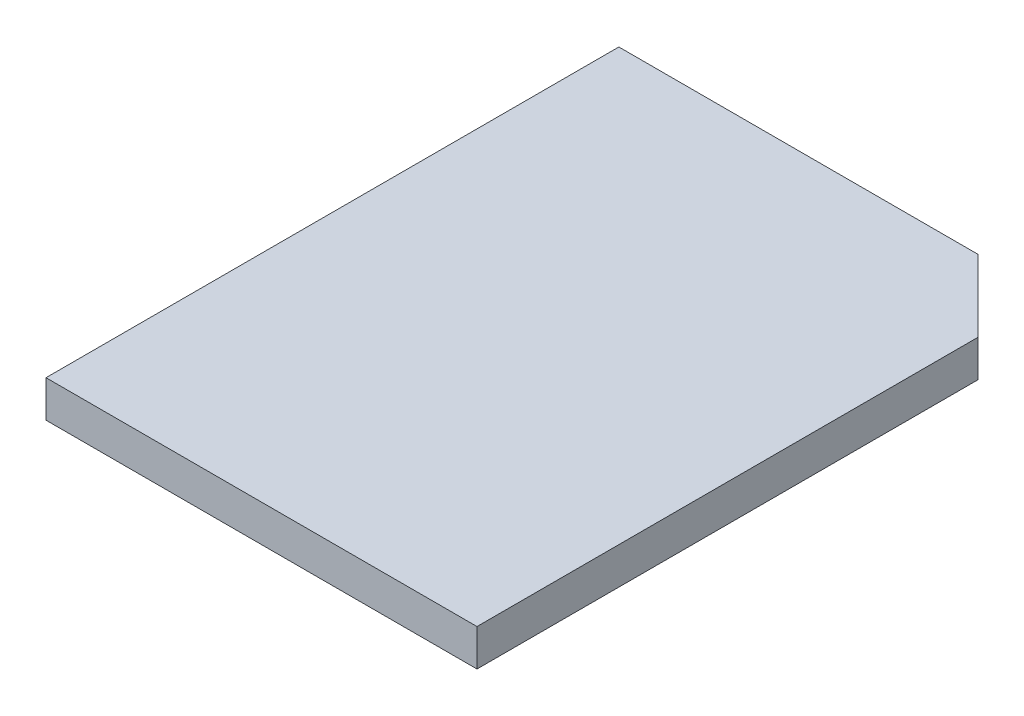
SolidWorks part; units mm, degrees
ref_plane "Alzado" through (0, 0, 0) normal (0, 0, 1) x (1, 0, 0)
ref_plane "Planta" through (0, 0, 0) normal (0, 1, 0) x (1, 0, 0)
ref_plane "Vista lateral" through (0, 0, 0) normal (1, 0, 0) x (0, 0, -1)
sketch "Croquis1" plane through (0, 0, 0) normal (0, 1, 0) x (1, 0, 0)
  line L0 (20, 31.9) -> (24, 27.9)
  line L1 (0, 0) -> (24, 0)
  line L2 (0, 0) -> (0, 31.9)
  line L3 (0, 31.9) -> (20, 31.9)
  line L4 (24, 0) -> (24, 27.9)
  dimension "D1" = 24
  dimension "D2" = 31.9
  dimension "D3" = 4
  dimension "D4" = 4
extrude "Saliente-Extruir1" add sketch "Croquis1" along normal blind 2.05
